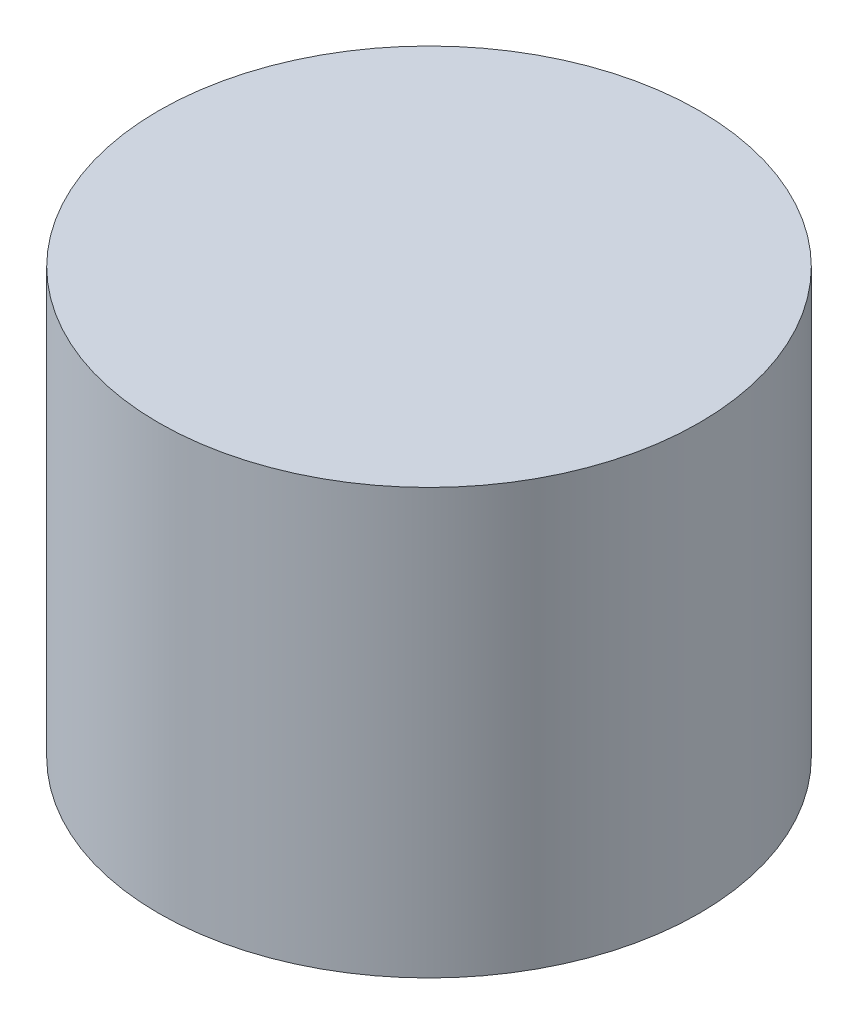
SolidWorks part; units mm, degrees
ref_plane "Front Plane" through (0, 0, 0) normal (0, 0, 1) x (1, 0, 0)
ref_plane "Top Plane" through (0, 0, 0) normal (0, 1, 0) x (1, 0, 0)
ref_plane "Right Plane" through (0, 0, 0) normal (1, 0, 0) x (0, 0, -1)
sketch "Sketch1" plane through (0, 0, 0) normal (0, 1, 0) x (1, 0, 0)
  circle A0 centre (0, 0) radius 14
extrude "Boss-Extrude1" add sketch "Sketch1" along normal blind 22
